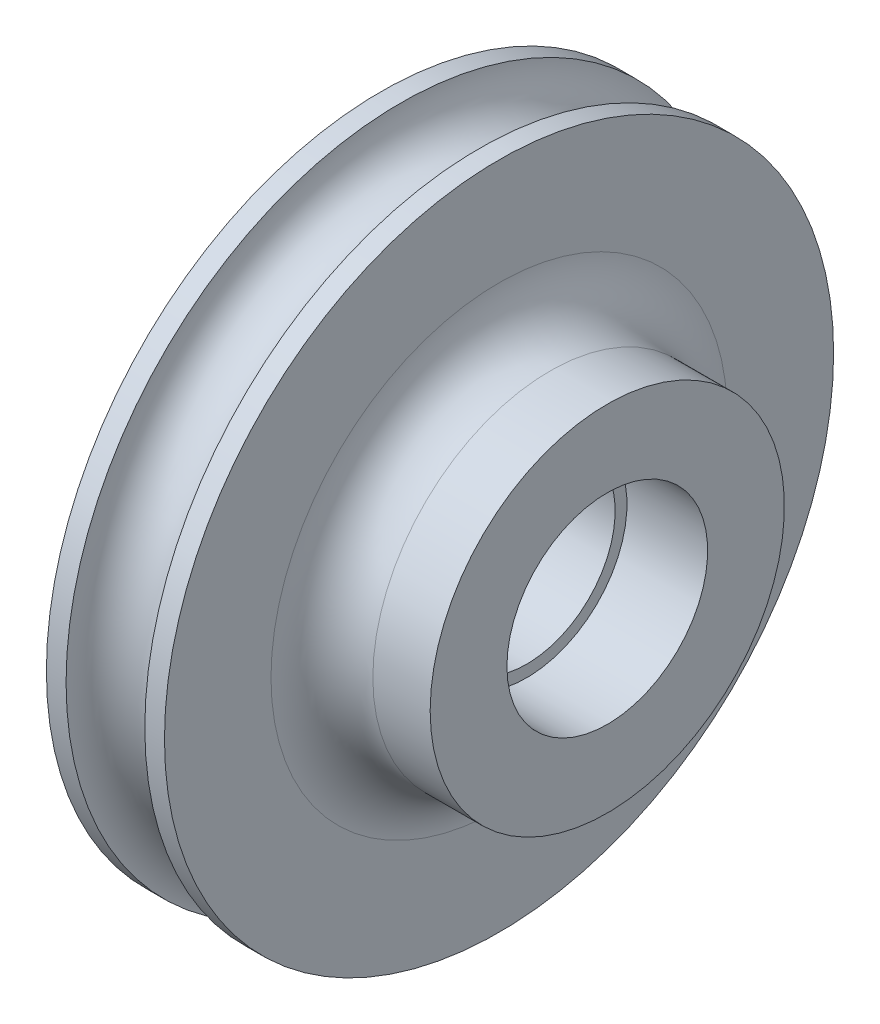
SolidWorks part; units mm, degrees
ref_plane "前视基准面" through (0, 0, 0) normal (0, 0, 1) x (1, 0, 0)
ref_plane "上视基准面" through (0, 0, 0) normal (0, 1, 0) x (1, 0, 0)
ref_plane "右视基准面" through (0, 0, 0) normal (1, 0, 0) x (0, 0, -1)
sketch "草图1" plane through (0, 0, 0) normal (0, 0, 1) x (1, 0, 0)
  line L0 (2, 17) -> (3, 17)
  line L1 (8.5, 9) -> (8.5, 5.1)
  line L2 (-3, 17) -> (-2, 17)
  line L3 (4.4, 4.5) -> (1.1, 4.5)
  line L4 (8.5, 9) -> (5.588, 9)
  line L5 (-3, 5.1) -> (1.1, 5.1)
  line L6 (1.1, 5.1) -> (1.1, 4.5)
  line L7 (0, 0) -> (4.8, 0) construction
  line L9 (8.5, 5.1) -> (4.4, 5.1)
  line L10 (4.4, 5.1) -> (4.4, 4.5)
  line L13 (3, 17) -> (3, 11.588)
  line L15 (-3, 17) -> (-3, 5.1)
  arc A0 (-2, 17) -> (2, 17) centre (0, 17) ccw
  arc A1 (5.588, 9) -> (3, 11.588) centre (5.588, 11.588) cw
  point P9 (-2, 5.1)
  dimension "D2" = 2.588
  dimension "D9" = 9
  dimension "D3" = 17
  dimension "D10" = 6
  dimension "D7" = 2
  dimension "D1" = 4
  dimension "D4" = 4.5
  dimension "D5" = 4.1
  dimension "D6" = 11.5
  dimension "D8" = 5.1
  dimension "D11" = 1
  dimension "D12" = 4.1
revolve "旋转1" add sketch "草图1" angle 360 about L7
